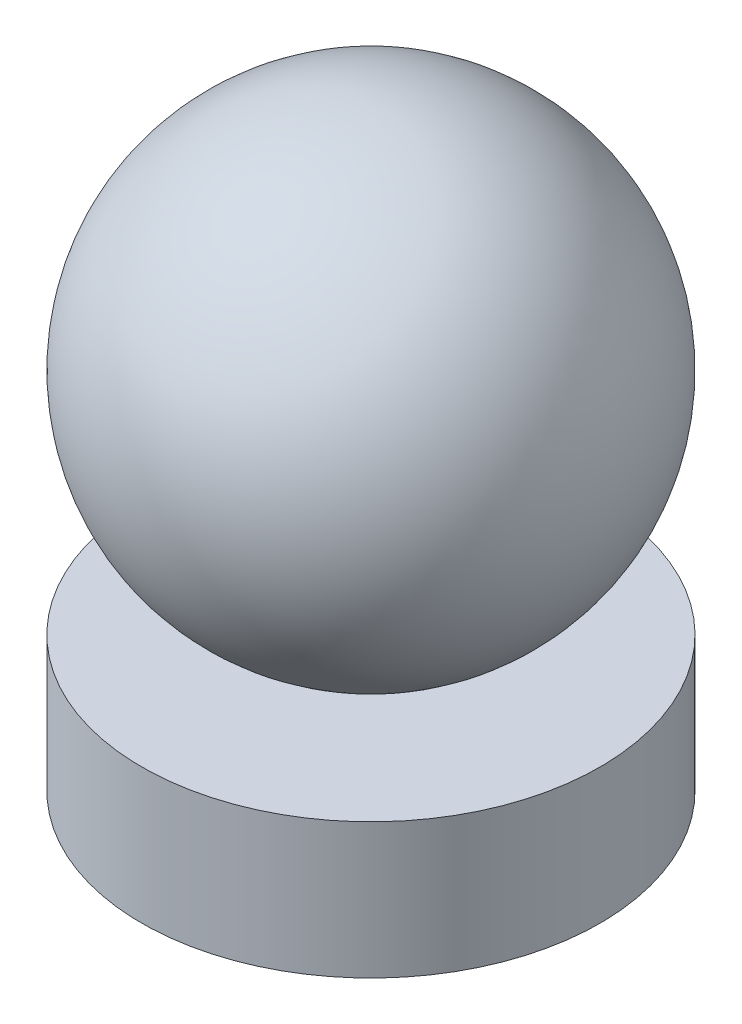
SolidWorks part; units mm, degrees
ref_plane "Front Plane" through (0, 0, 0) normal (0, 0, 1) x (1, 0, 0)
ref_plane "Top Plane" through (0, 0, 0) normal (0, 1, 0) x (1, 0, 0)
ref_plane "Right Plane" through (0, 0, 0) normal (1, 0, 0) x (0, 0, -1)
sketch "Sketch1" plane through (0, 0, 0) normal (0, 0, 1) x (1, 0, 0)
  line L0 (0, 1.875) -> (0, 8.225)
  line L2 (0, 0) -> (3.175, 0)
  line L3 (0, 0) -> (0, 1.875)
  line L4 (0, 1.875) -> (3.175, 1.875)
  line L5 (3.175, 0) -> (3.175, 1.875)
  arc A0 (0, 8.225) -> (0, 1.875) centre (0, 5.05) cw
  dimension "D1" = 6.35
revolve "Revolve1" add sketch "Sketch1" angle 360 about L3
